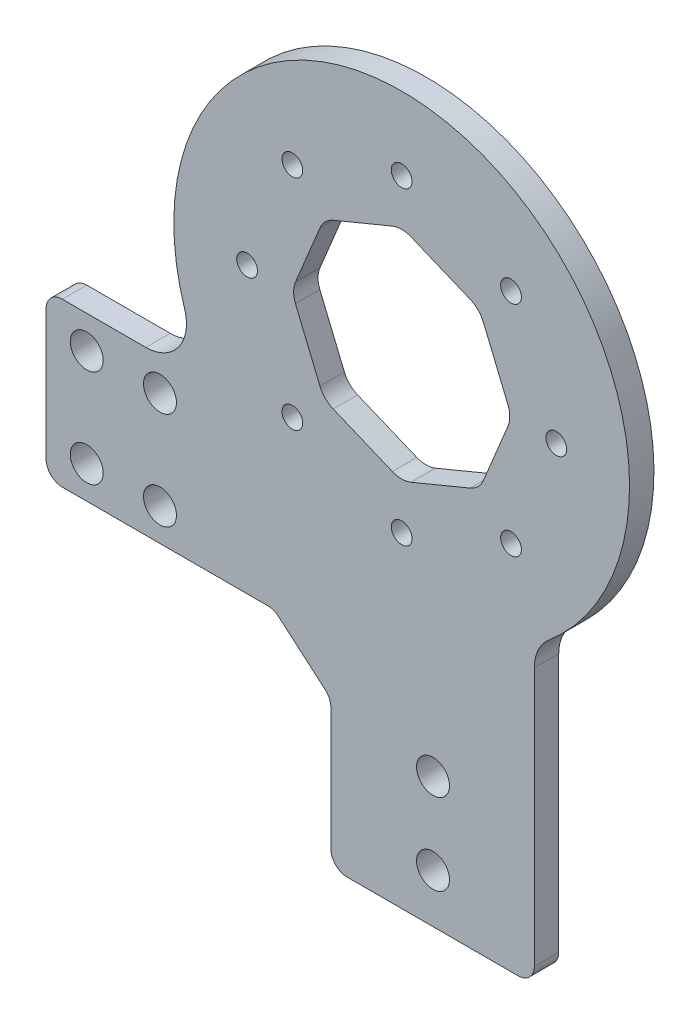
SolidWorks part; units mm, degrees
material "Thornel Mat VMA"
ref_plane "前视基准面" through (0, 0, 0) normal (0, 0, 1) x (1, 0, 0)
ref_plane "上视基准面" through (0, 0, 0) normal (0, 1, 0) x (1, 0, 0)
ref_plane "右视基准面" through (0, 0, 0) normal (1, 0, 0) x (0, 0, -1)
other "Configuration Table"
sketch "草图1" plane through (0, 0, 0) normal (0, 0, 1) x (1, 0, 0)
  line L0 (0, 0) -> (0, 24)
  line L1 (0, 24) -> (-7, 30)
  line L2 (-7, 30) -> (-35, 30)
  line L3 (-35, 30) -> (-35, 50)
  line L4 (-35, 50) -> (25, 50)
  line L5 (25, 50) -> (25, 0)
  line L6 (25, 0) -> (0, 0)
  dimension "D1" = 25
  dimension "D2" = 7
  dimension "D3" = 6
  dimension "D4" = 50
  dimension "D5" = 60
  dimension "D6" = 20
extrude "凸台-拉伸1" add sketch "草图1" along normal mid plane 3
sketch "草图2" plane through (0, 0, 1.5) normal (0, 0, 1) x (1, 0, 0)
  line L0 (-35, 30) -> (-7, 30) construction
  line L1 (25, 0) -> (25, 50) construction
  circle A0 centre (8.7, 65) radius 28
  dimension "D3" = 56
  dimension "D1" = 35
  dimension "D2" = 16.3
extrude "凸台-拉伸2" add sketch "草图2" against normal up to surface (3 mm away) up to face at (-3.8571, 26.2857, -1.5)
fillet "圆角1" radius 2 6 edges at (25, 0, 0) (0, 0, 0) (0, 24, 0) (-7, 30, 0) (-35, 30, 0) (-35, 50, 0)
sketch "草图3" plane through (0, 0, 1.5) normal (0, 0, 1) x (1, 0, 0)
  line L0 (8.7, 65) -> (22.135, 78.435) construction
  line L1 (8.7, 65) -> (27.7, 65) construction
  circle A0 centre (8.7, 65) radius 19 construction
  circle A1 centre (22.135, 78.435) radius 1.275
  circle A2 centre (27.7, 65) radius 1.275
  circle A3 centre (22.135, 51.565) radius 1.275
  circle A4 centre (8.7, 46) radius 1.275
  circle A5 centre (-4.735, 51.565) radius 1.275
  circle A6 centre (-10.3, 65) radius 1.275
  circle A7 centre (-4.735, 78.435) radius 1.275
  circle A8 centre (8.7, 84) radius 1.275
  arc A9 (25, 42.2336) -> (-14.9432, 50) centre (8.7, 65) ccw construction
  point P22 (8.7, 65)
  dimension "D1" = 38
  dimension "D2" = 2.55
  dimension "D3" = 45
  dimension "D4" = 8
extrude "切除-拉伸1" cut sketch "草图3" against normal through all
sketch "草图4" plane through (0, 0, 1.5) normal (0, 0, 1) x (1, 0, 0)
  line L0 (-33, 30) -> (-7.7398, 30) construction
  line L1 (7.55, 22) -> (17.55, 22) construction
  line L2 (7.55, 22) -> (7.55, 12) construction
  line L3 (7.55, 12) -> (17.55, 12) construction
  line L4 (17.55, 22) -> (17.55, 12) construction
  line L5 (0, 23.0801) -> (0, 2) construction
  circle A4 centre (12.55, 22) radius 2.025
  circle A5 centre (12.55, 12) radius 2.025
  dimension "D1" = 4.05
  dimension "D2" = 10
  dimension "D3" = 7.55
  dimension "D4" = 8
  dimension "D5" = 10
extrude "切除-拉伸2" cut sketch "草图4" against normal through all
sketch "草图5" plane through (0, 0, 1.5) normal (0, 0, 1) x (1, 0, 0)
  line L0 (0, 23.0801) -> (0, 2) construction
  line L1 (0, 6) -> (25, 6)
  line L2 (0, 6) -> (0, 0)
  line L3 (0, 0) -> (25, 0)
  line L4 (25, 6) -> (25, 0)
  line L5 (25, 2) -> (25, 42.2336) construction
  line L6 (2, 0) -> (23, 0) construction
  dimension "D1" = 6
extrude "切除-拉伸3" cut sketch "草图5" against normal through all
fillet "圆角2" radius 2 2 edges at (25, 6, 0) (0, 6, 0)
sketch "草图6" plane through (0, 0, 1.5) normal (0, 0, 1) x (1, 0, 0)
  line L0 (-30, 46) -> (-30, 34) construction
  line L1 (-35, 48) -> (-35, 32) construction
  line L2 (-33, 30) -> (-7.7398, 30) construction
  circle A0 centre (-30, 46) radius 2.025
  circle A1 centre (-30, 34) radius 2.025
  dimension "D1" = 4.05
  dimension "D2" = 5
  dimension "D3" = 4
  dimension "D4" = 12
extrude "切除-拉伸4" cut sketch "草图6" against normal blind 10
fillet "圆角3" radius 5 2 edges at (25, 42.2336, 0) (-14.9432, 50, 0)
sketch "草图7" plane through (0, 0, 1.5) normal (0, 0, 1) x (1, 0, 0)
  line L1 (-30, 46) -> (-21, 46) construction
  line L2 (-30, 46) -> (-30, 34) construction
  line L3 (-30, 34) -> (-21, 34) construction
  line L4 (-21, 46) -> (-21, 34) construction
  circle A0 centre (-30, 34) radius 2.025 construction
  circle A1 centre (-21, 46) radius 2.025
  circle A2 centre (-21, 34) radius 2.025
  dimension "D2" = 4.05
  dimension "D1" = 9
extrude "切除-拉伸5" cut sketch "草图7" against normal through all both
sketch "草图8" plane through (0, 0, 1.5) normal (0, 0, 1) x (1, 0, 0)
  line L1 (8.7, 78.5299) -> (-0.8671, 74.5671)
  line L2 (-0.8671, 74.5671) -> (-4.8299, 65)
  line L3 (-4.8299, 65) -> (-0.8671, 55.4329)
  line L4 (-0.8671, 55.4329) -> (8.7, 51.4701)
  line L5 (8.7, 51.4701) -> (18.2671, 55.4329)
  line L6 (18.2671, 55.4329) -> (22.2299, 65)
  line L7 (22.2299, 65) -> (18.2671, 74.5671)
  line L8 (18.2671, 74.5671) -> (8.7, 78.5299)
  circle A0 centre (8.7, 65) radius 12.5 construction
  point P1 (0, 0)
  point P12 (0, 0)
  dimension "D1" = 25
extrude "切除-拉伸6" cut sketch "草图8" against normal blind 10
fillet "圆角4" radius 3 8 edges at (18.2671, 74.5671, 0) (22.2299, 65, 0) (18.2671, 55.4329, 0) (8.7, 51.4701, 0) (-0.8671, 55.4329, 0) (-0.8671, 74.5671, 0) (8.7, 78.5299, 0) (-4.8299, 65, 0)
